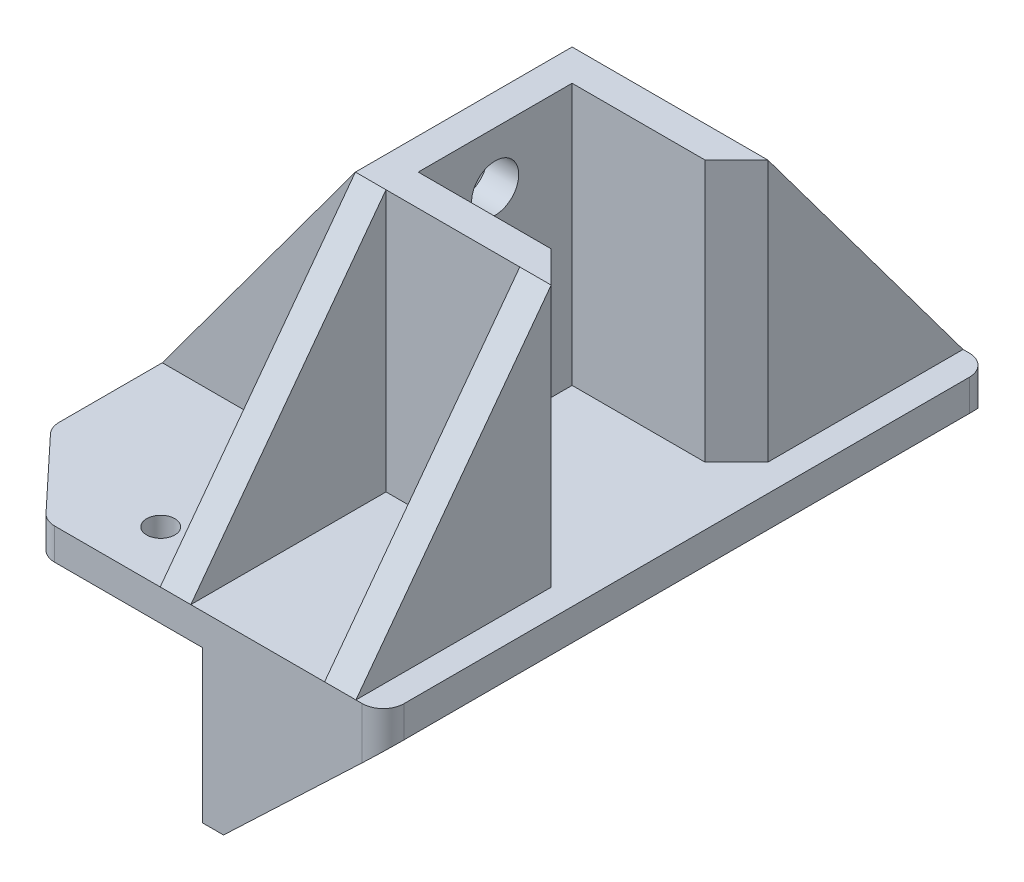
SolidWorks part; units mm, degrees
ref_plane "Front Plane" through (0, 0, 0) normal (0, 0, 1) x (1, 0, 0)
ref_plane "Top Plane" through (0, 0, 0) normal (0, 1, 0) x (1, 0, 0)
ref_plane "Right Plane" through (0, 0, 0) normal (1, 0, 0) x (0, 0, -1)
sketch "Sketch1" plane through (0, 0, 0) normal (0, 1, 0) x (1, 0, 0)
  line L1 (-18.375, -29) -> (18.375, -29)
  line L2 (-18.375, -29) -> (-18.375, 29)
  line L3 (-18.375, 29) -> (18.375, 29)
  line L4 (18.375, -29) -> (18.375, 29)
  line L5 (-18.375, -29) -> (18.375, 29) construction
  line L6 (-18.375, 29) -> (18.375, -29) construction
  point P0 (0, 0)
  dimension "D1" = 58
  dimension "D2" = 36.75
extrude "Boss-Extrude1" add sketch "Sketch1" along normal blind 3
sketch "Sketch2" plane through (0, 0, 0) normal (0, -1, 0) x (1, 0, 0)
  line L0 (-18.375, 29) -> (18.375, 29) construction
  line L1 (1.125, 29) -> (3.125, 29)
  line L2 (1.125, 29) -> (1.125, 19)
  line L3 (1.125, 19) -> (3.125, 19)
  line L4 (3.125, 29) -> (3.125, 19)
  line L5 (18.375, 29) -> (18.375, -29) construction
  line L6 (1.65, 0) -> (-1.65, 0) construction
  line L7 (1.125, -19) -> (3.125, -19)
  line L8 (3.125, -29) -> (3.125, -19)
  line L9 (1.125, -29) -> (3.125, -29)
  line L10 (1.125, -29) -> (1.125, -19)
  dimension "D1" = 2
  dimension "D2" = 15.25
  dimension "D3" = 10
extrude "Boss-Extrude2" add sketch "Sketch2" along normal blind 14.5
sketch "Sketch3" plane through (3.125, 0, 0) normal (1, 0, 0) x (0, 0, -1)
  line L0 (-19, -14.5) -> (-29, -14.5) construction
  line L1 (-19, -14.5) -> (-19, 0) construction
  line L2 (0, 1.65) -> (0, -1.65) construction
  circle A0 centre (-24, -9) radius 1.35
  circle A1 centre (24, -9) radius 1.35
  dimension "D1" = 2.7
  dimension "D2" = 5.5
  dimension "D3" = 5
extrude "Cut-Extrude1" cut sketch "Sketch3" against normal up to surface (2 mm away) up to face at (1.125, -7.25, -24)
sketch "Sketch4" plane through (0, 3, 0) normal (0, 1, 0) x (1, 0, 0)
  line L0 (18.375, -29) -> (18.375, 29) construction
  line L1 (12.775, 7.35) -> (0.075, 7.35)
  line L3 (12.775, -7.35) -> (0.075, -7.35)
  line L4 (0.075, 7.35) -> (0.075, -7.35)
  line L5 (15.775, 10.35) -> (-2.925, 10.35)
  line L6 (-2.925, 10.35) -> (-2.925, -10.35)
  line L7 (15.775, -10.35) -> (-2.925, -10.35)
  line L9 (12.775, 7.35) -> (15.775, 10.35)
  line L10 (12.775, -7.35) -> (15.775, -10.35)
  line L12 (15.775, 10.35) -> (15.775, -10.35) construction
  line L13 (12.775, 7.35) -> (12.775, -7.35) construction
  dimension "D1" = 12.7
  dimension "D2" = 14.7
  dimension "D3" = 7.35
  dimension "D4" = 18.3
  dimension "D6" = 20.7
  dimension "D5" = 3
extrude "Boss-Extrude3" add sketch "Sketch4" along normal blind 25
sketch "Sketch5" plane through (-2.925, 0, 0) normal (-1, 0, 0) x (0, 0, 1)
  line L0 (-29, 3) -> (29, 3) construction
  circle A0 centre (0, 8) radius 2.25
  circle A1 centre (0, 23) radius 2.25
  point P5 (0, 3)
  dimension "D1" = 4.5
  dimension "D2" = 5
  dimension "D3" = 2
extrude "Cut-Extrude2" cut sketch "Sketch5" against normal up to surface (3 mm away) up to face at (0.075, 15.5, 0)
sketch "Sketch6" plane through (-18.375, 0, 0) normal (-1, 0, 0) x (0, 0, 1)
  line L1 (-29, 3) -> (29, 3)
  line L2 (-29, 3) -> (-29, 0)
  line L3 (-29, 0) -> (29, 0)
  line L4 (29, 3) -> (29, 0)
extrude "Boss-Extrude4" add sketch "Sketch6" along normal blind 3
sketch "Sketch7" plane through (0, 3, 0) normal (0, 1, 0) x (1, 0, 0)
  line L0 (-21.375, -29) -> (-21.375, 29) construction
  circle A0 centre (-11.375, 0) radius 6
  dimension "D1" = 12
  dimension "D2" = 10
extrude "Cut-Extrude3" cut sketch "Sketch7" against normal up to surface (3 mm away) up to face at (0.9167, 0, 0)
sketch "Sketch8" plane through (0, 3, 0) normal (0, 1, 0) x (1, 0, 0)
  line L0 (-21.375, 21) -> (-21.375, -21)
  line L1 (-21.375, -29) -> (-21.375, 29) construction
  line L2 (-21.375, -21) -> (-13.875, -29)
  line L3 (-21.375, -29) -> (18.375, -29) construction
  line L4 (-21.375, 21) -> (-13.875, 29)
  line L5 (18.375, 29) -> (-21.375, 29) construction
  line L6 (-13.875, 29) -> (-13.875, 36.079)
  line L7 (-13.875, 36.079) -> (-41.6424, 35.784)
  line L8 (-41.6424, 35.784) -> (-32.6375, -32.5866)
  line L9 (-32.6375, -32.5866) -> (-11.2438, -32.5866)
  line L10 (-11.2438, -32.5866) -> (-13.875, -29)
  point P5 (-21.375, 0)
  dimension "D1" = 42
  dimension "D2" = 0
  dimension "D3" = 7.5
extrude "Cut-Extrude4" cut sketch "Sketch8" against normal up to surface (3 mm away) up to face at (-11.375, 0, -6)
sketch "Sketch9" plane through (3.125, 0, 0) normal (1, 0, 0) x (0, 0, -1)
  line L0 (29, 0) -> (19, 0) construction
  line L1 (19, -14.5) -> (21, -14.5)
  line L2 (19, -14.5) -> (19, 0)
  line L3 (19, 0) -> (21, 0)
  line L4 (21, -14.5) -> (21, 0)
  line L5 (-29, 0) -> (29, 0) construction
  line L6 (29, -14.5) -> (27, -14.5)
  line L7 (29, -14.5) -> (29, 0)
  line L8 (29, 0) -> (27, 0)
  line L9 (27, -14.5) -> (27, 0)
  line L10 (0, 9.625) -> (0, -9.625) construction
  line L11 (-29, 0) -> (-27, 0)
  line L12 (-27, -14.5) -> (-27, 0)
  line L13 (-29, -14.5) -> (-27, -14.5)
  line L14 (-29, -14.5) -> (-29, 0)
  line L15 (-19, 0) -> (-21, 0)
  line L16 (-21, -14.5) -> (-21, 0)
  line L17 (-19, -14.5) -> (-21, -14.5)
  line L18 (-19, -14.5) -> (-19, 0)
  dimension "D1" = 2
  dimension "D2" = 2
extrude "Boss-Extrude5" add sketch "Sketch9" along normal up to surface (15.25 mm away) up to face at (18.375, 1.5, 0)
sketch "Sketch10" plane through (0, 0, 27) normal (0, 0, -1) x (-1, 0, 0)
  line L0 (-18.375, 0) -> (-3.125, -14.5)
  line L1 (-18.375, 3) -> (-18.375, -14.5) construction
  line L2 (-3.125, -14.5) -> (-3.8181, -23.1756)
  line L3 (-3.8181, -23.1756) -> (-24.2993, -22.1354)
  line L4 (-24.2993, -22.1354) -> (-27.6872, 0.8557)
  line L5 (-27.6872, 0.8557) -> (-18.375, 0)
extrude "Cut-Extrude5" cut sketch "Sketch10" against normal mid plane 160
sketch "Sketch11" plane through (0, 0, 0) normal (0, -1, 0) x (1, 0, 0)
  line L0 (-21.375, -21) -> (-21.375, 21) construction
  line L1 (-13.875, 29) -> (1.125, 29) construction
  line L2 (9.625, 0) -> (-9.625, 0) construction
  circle A0 centre (-7.875, 24) radius 1.35
  circle A1 centre (-7.875, -24) radius 1.35
  dimension "D1" = 2.7
  dimension "D2" = 13.5
  dimension "D3" = 5
extrude "Cut-Extrude6" cut sketch "Sketch11" against normal up to surface (3 mm away) up to face at (-11.375, 3, 6)
fillet "Fillet1" radius 2 6 edges at (-21.375, 1.5, 21) (-13.875, 1.5, 29) (-21.375, 1.5, -21) (-13.875, 1.5, -29) (18.375, 1.5, 29) (18.375, 1.5, -29)
sketch "Sketch12" plane through (0, 3, 0) normal (0, 1, 0) x (1, 0, 0)
  line L0 (-13.0085, -29) -> (16.375, -29) construction
  line L1 (-2.925, -10.35) -> (0, -10.35)
  line L2 (-2.925, -10.35) -> (-2.925, -29)
  line L3 (-2.925, -29) -> (0, -29)
  line L4 (0, -10.35) -> (0, -29)
  line L5 (-9.625, 0) -> (9.625, 0) construction
  line L6 (15.775, -10.35) -> (12.7778, -10.35)
  line L7 (15.775, -10.35) -> (15.775, -29)
  line L8 (15.775, -29) -> (12.7778, -29)
  line L9 (12.7778, -10.35) -> (12.7778, -29)
  line L10 (-2.925, 29) -> (0, 29)
  line L11 (0, 10.35) -> (0, 29)
  line L12 (-2.925, 10.35) -> (0, 10.35)
  line L13 (-2.925, 10.35) -> (-2.925, 29)
  line L14 (15.775, 29) -> (12.7778, 29)
  line L15 (12.7778, 10.35) -> (12.7778, 29)
  line L16 (15.775, 10.35) -> (12.7778, 10.35)
  line L17 (15.775, 10.35) -> (15.775, 29)
extrude "Boss-Extrude6" add sketch "Sketch12" along normal up to surface (25 mm away) up to face at (6.425, 28, 0)
sketch "Sketch13" plane through (15.775, 0, 0) normal (1, 0, 0) x (0, 0, -1)
  line L0 (-10.35, 28) -> (-29, 3)
  line L1 (-29, 3) -> (-37.6177, 3)
  line L2 (-37.6177, 3) -> (-37.6177, 32.3915)
  line L3 (-37.6177, 32.3915) -> (-10.35, 32.3915)
  line L4 (-10.35, 32.3915) -> (-10.35, 28)
  line L5 (0, 9.625) -> (0, -9.625) construction
  line L6 (37.6177, 32.3915) -> (10.35, 32.3915)
  line L7 (37.6177, 3) -> (37.6177, 32.3915)
  line L8 (29, 3) -> (37.6177, 3)
  line L9 (10.35, 28) -> (29, 3)
  line L10 (10.35, 32.3915) -> (10.35, 28)
extrude "Cut-Extrude7" cut sketch "Sketch13" against normal up to surface (18.7 mm away) up to face at (-2.925, 8, 2.25)
sketch "Sketch14" plane through (0, 3, 0) normal (0, 1, 0) x (1, 0, 0)
  line L0 (-21.375, -20.2091) -> (-21.375, 20.2091) construction
  line L1 (-2.925, 10.35) -> (-21.375, 10.35)
  line L2 (-2.925, 10.35) -> (-2.925, 6.35)
  line L3 (-2.925, 6.35) -> (-21.375, 6.35)
  line L4 (-21.375, 10.35) -> (-21.375, 6.35)
  line L5 (-9.625, 0) -> (9.625, 0) construction
  line L6 (-2.925, -6.35) -> (-21.375, -6.35)
  line L7 (-21.375, -10.35) -> (-21.375, -6.35)
  line L8 (-2.925, -10.35) -> (-21.375, -10.35)
  line L9 (-2.925, -10.35) -> (-2.925, -6.35)
extrude "Boss-Extrude7" add sketch "Sketch14" along normal up to surface (25 mm away) up to face at (6.413, 28, 0)
sketch "Sketch15" plane through (0, 0, 10.35) normal (0, 0, 1) x (1, 0, 0)
  line L0 (-2.925, 28) -> (-21.375, 3)
  line L1 (-21.375, 3) -> (-26.9603, 3)
  line L2 (-26.9603, 3) -> (-26.9603, 29.4017)
  line L3 (-26.9603, 29.4017) -> (-2.925, 29.4017)
  line L4 (-2.925, 29.4017) -> (-2.925, 28)
extrude "Cut-Extrude8" cut sketch "Sketch15" against normal up to surface (20.7 mm away) up to face at (-12.15, 15.5, -10.35)
